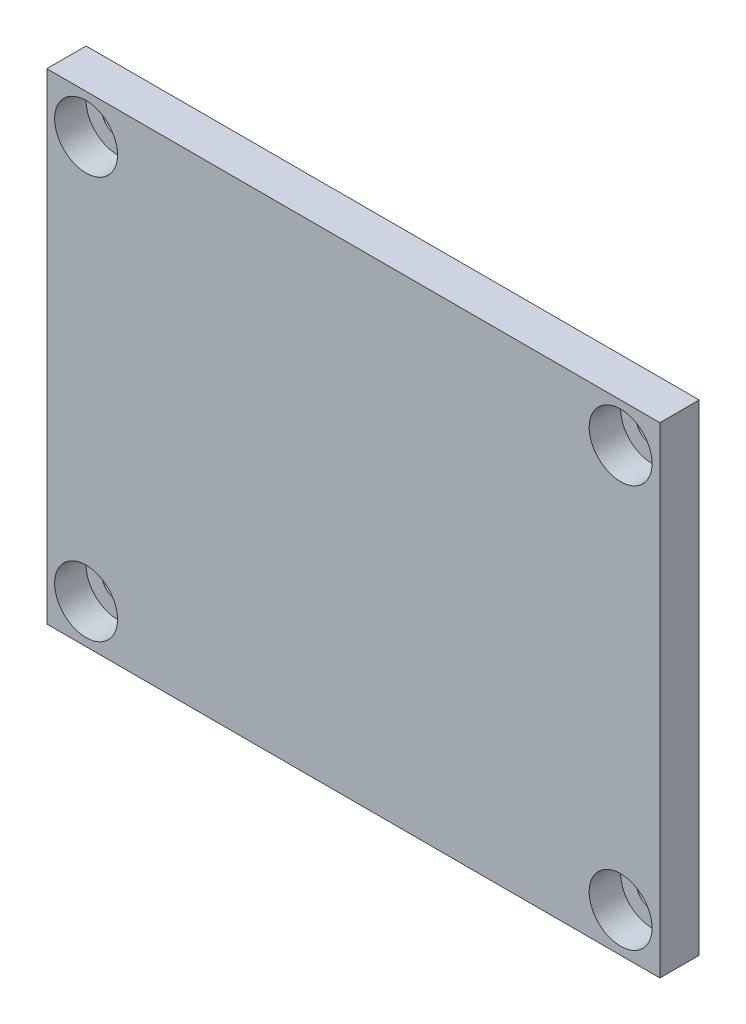
SolidWorks part; units mm, degrees
ref_plane "前视基准面" through (0, 0, 0) normal (0, 0, 1) x (1, 0, 0)
ref_plane "上视基准面" through (0, 0, 0) normal (0, 1, 0) x (1, 0, 0)
ref_plane "右视基准面" through (0, 0, 0) normal (1, 0, 0) x (0, 0, -1)
sketch "草图1" plane through (0, 0, 0) normal (0, 0, 1) x (1, 0, 0)
  line L0 (0, 0) -> (39, 0)
  line L1 (39, 0) -> (39, 30.59)
  line L2 (39, 30.59) -> (0, 30.59)
  line L3 (0, 30.59) -> (0, 0)
  dimension "D1" = 39
  dimension "D2" = 30.59
extrude "凸台-拉伸1" add sketch "草图1" against normal blind 2.5
sketch "草图2" plane through (0, 0, 0) normal (0, 0, 1) x (1, 0, 0)
  line L0 (0, 5) -> (5, 5)
  line L1 (0, 30.59) -> (0, 0) construction
  line L2 (5, 5) -> (5, 0)
  line L3 (0, 0) -> (39, 0) construction
  line L4 (5, 0) -> (0, 0)
  line L5 (0, 0) -> (0, 5)
  line L6 (34, 30.59) -> (34, 25.59)
  line L7 (39, 30.59) -> (0, 30.59) construction
  line L8 (34, 25.59) -> (39, 25.59)
  line L9 (39, 0) -> (39, 30.59) construction
  line L10 (39, 25.59) -> (39, 30.59)
  line L11 (39, 30.59) -> (34, 30.59)
  dimension "D1" = 5
  dimension "D2" = 5
  dimension "D3" = 5
  dimension "D4" = 5
extrude "凸台-拉伸2" add sketch "草图2" against normal blind 2.5
sketch "草图3" plane through (0, 0, 0) normal (0, 0, 1) x (1, 0, 0)
  line L8 (5, 5) -> (0, 0) construction
  line L9 (0, 5) -> (5, 0) construction
  line L10 (34, 30.59) -> (39, 25.59) construction
  line L11 (34, 25.59) -> (39, 30.59) construction
hole_wizard "M2 六角头螺栓的柱形沉头孔8" positions "3D草图1" profile "草图4" size "M2" standard "GB" slot yes
sketch3d "3D草图1"
  line L0 (5, 5, 0) -> (0, 0, 0) construction
  line L1 (34, 30.59, 0) -> (39, 25.59, 0) construction
  point P0 (2.5, 2.5, 0)
  point P4 (36.5, 28.09, 0)
  point P9 (2.5, 2.5, 0)
  point P11 (36.5, 28.09, 0)
sketch "草图4" plane through (2.5, 2.5, 0) normal (1, 0, 0) x (0, -1, 0)
  line L0 (0, 0) -> (0, 3)
  line L1 (0, 3) -> (1, 3)
  line L2 (1, 3) -> (1, 2)
  line L3 (1, 2) -> (2, 2)
  line L4 (2, 2) -> (2, 0)
  line L5 (2, 0) -> (0, 0)
  line L10 (0, 3) -> (-1, 3) construction
  line L11 (0, -6.35) -> (0, 107.95) construction
  dimension "孔直径" = 2
  dimension "孔深度" = 3
  dimension "柱形沉头孔直径" = 4
  dimension "柱形沉头孔深度" = 2
  dimension "导头角度" = 180
hole_wizard "M2 六角头螺栓的柱形沉头孔7" positions "草图5" profile "草图6" size "M2" standard "GB" slot yes
sketch "草图5" plane through (0, 0, 0) normal (0, 0, 1) x (1, 0, 0)
  line L0 (2.5, 2.5) -> (2.5, 32.4921) construction
  line L1 (0, 5) -> (5, 0) construction
  line L3 (2.5, 2.5) -> (43.7133, 2.5) construction
  line L5 (36.5, 28.09) -> (-2.3957, 28.09) construction
  line L6 (34, 30.59) -> (39, 25.59) construction
  line L8 (36.5, 28.09) -> (36.5, -0.6026) construction
  point P0 (2.5, 28.09)
  point P2 (36.5, 2.5)
sketch "草图6" plane through (2.5, 28.09, 0) normal (1, 0, 0) x (0, -1, 0)
  line L0 (0, 0) -> (0, 3)
  line L1 (0, 3) -> (1, 3)
  line L2 (1, 3) -> (1, 2)
  line L3 (1, 2) -> (2, 2)
  line L4 (2, 2) -> (2, 0)
  line L5 (2, 0) -> (0, 0)
  line L10 (0, 3) -> (-1, 3) construction
  line L11 (0, -6.35) -> (0, 107.95) construction
  dimension "孔直径" = 2
  dimension "孔深度" = 3
  dimension "柱形沉头孔直径" = 4
  dimension "柱形沉头孔深度" = 2
  dimension "导头角度" = 180
